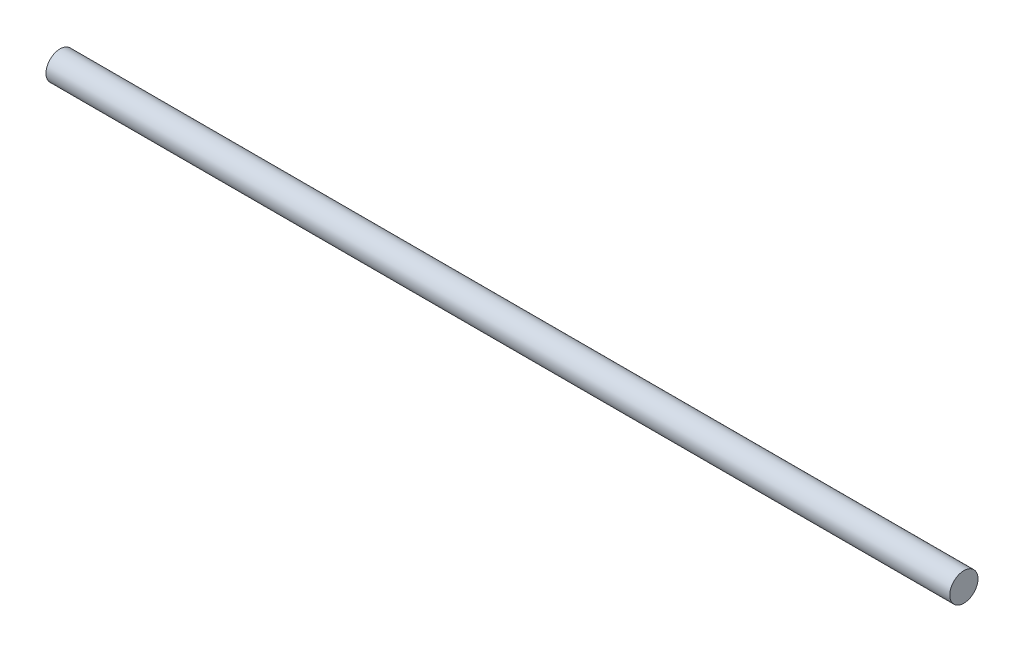
SolidWorks part; units mm, degrees
material "Rubber"
ref_plane "Front Plane" through (0, 0, 0) normal (0, 0, 1) x (1, 0, 0)
ref_plane "Top Plane" through (0, 0, 0) normal (0, 1, 0) x (1, 0, 0)
ref_plane "Right Plane" through (0, 0, 0) normal (1, 0, 0) x (0, 0, -1)
sketch "MuscleDiameter" plane through (0, 0, 0) normal (1, 0, 0) x (0, 0, -1)
  circle A0 centre (0, 0) radius 12.5
  dimension "D1" = 25
extrude "MuscleLength" add sketch "MuscleDiameter" along normal blind 800 contours A0
equation "\"MuscleLength\"=800"
equation "\"MuscleLen@MuscleLength\"=\"MuscleLen@Flying Platform.SLDASM\""
equation "\"D1@MuscleDiameter\" =  - 0.1 * \"MuscleLen@MuscleLength\" + 105"
